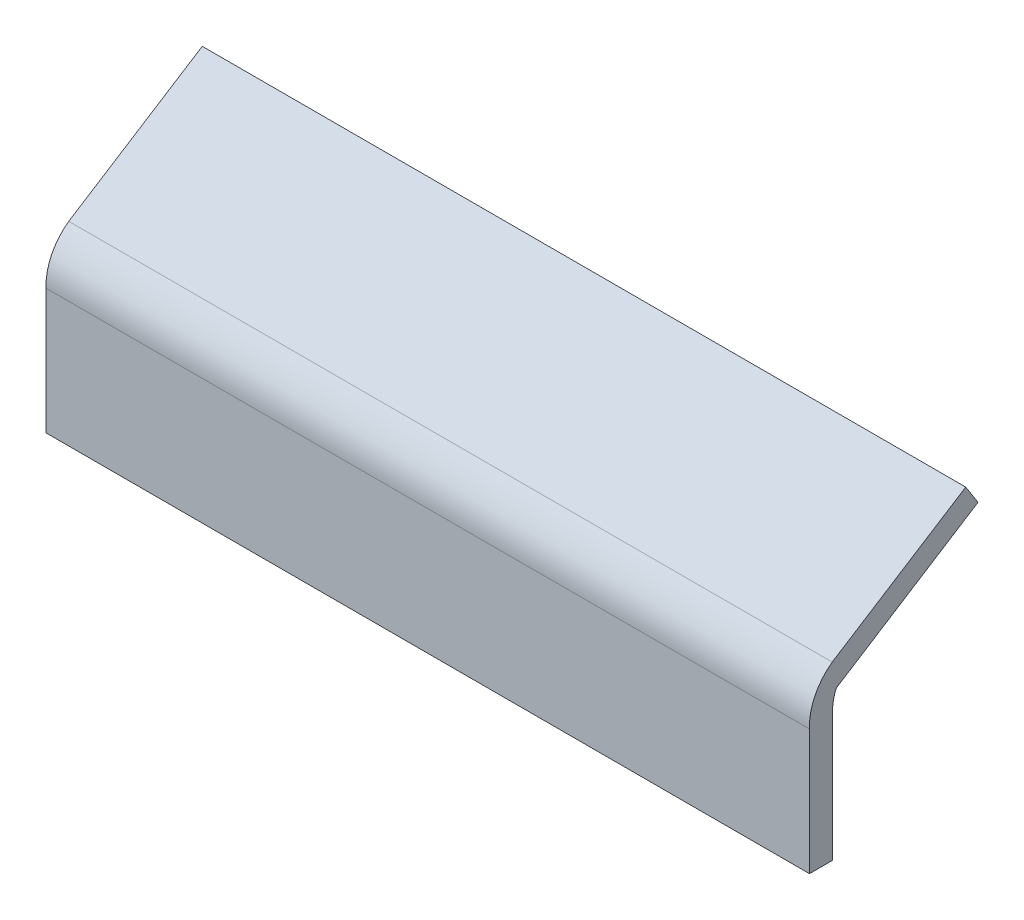
SolidWorks part; units mm, degrees
ref_plane "Front" through (0, 0, 0) normal (0, 0, 1) x (1, 0, 0)
ref_plane "Top" through (0, 0, 0) normal (0, 1, 0) x (1, 0, 0)
ref_plane "Right" through (0, 0, 0) normal (1, 0, 0) x (0, 0, -1)
sketch "Sketch1" plane through (0, 0, 0) normal (0, 0, 1) x (1, 0, 0)
  line L1 (557.5, 91.5) -> (-557.5, 91.5)
  line L2 (557.5, 91.5) -> (557.5, -91.5)
  line L3 (557.5, -91.5) -> (-557.5, -91.5)
  line L4 (-557.5, 91.5) -> (-557.5, -91.5)
  line L5 (557.5, 91.5) -> (-557.5, -91.5) construction
  line L6 (557.5, -91.5) -> (-557.5, 91.5) construction
  point P0 (0, 0)
  dimension "D1" = 1115
  dimension "D2" = 183
extrude "Boss-Extrude1" add sketch "Sketch1" along normal blind 33.45
sketch "Sketch2" plane through (557.5, 0, 0) normal (1, 0, 0) x (0, 0, -1)
  line L0 (-0.2363, 159.5152) -> (194.7791, 283.3295)
  line L1 (17.6927, 131.2759) -> (212.7081, 255.0903) construction
  line L2 (194.7791, 283.3295) -> (212.7081, 255.0903)
  line L3 (8.2042, 125.2517) -> (212.7081, 255.0903)
  line L4 (-33.45, 91.5) -> (0, 91.5) construction
  line L5 (-33.45, 91.5) -> (0, 91.5)
  arc A0 (-33.45, 91.5) -> (-0.2363, 159.5152) centre (46.4907, 94.5799) cw
  arc A1 (0, 91.5) -> (4.0818, 119.9852) centre (79.9407, 94.5799) cw
  arc A2 (8.2042, 125.2517) -> (4.0818, 119.9852) centre (13.5642, 116.8095) ccw
  dimension "D1" = 80
  dimension "D4" = 10
  dimension "D5" = 80
  dimension "D2" = 231
  dimension "D3" = 33.45
  dimension "D6" = 242.2393
  dimension "D7" = 163.5903
  dimension "D8" = 33.2137
  dimension "D9" = 28.4852
extrude "Boss-Extrude2" add sketch "Sketch2" against normal up to surface (1115 mm away) up to face at (-557.5, 0, 16.725)
